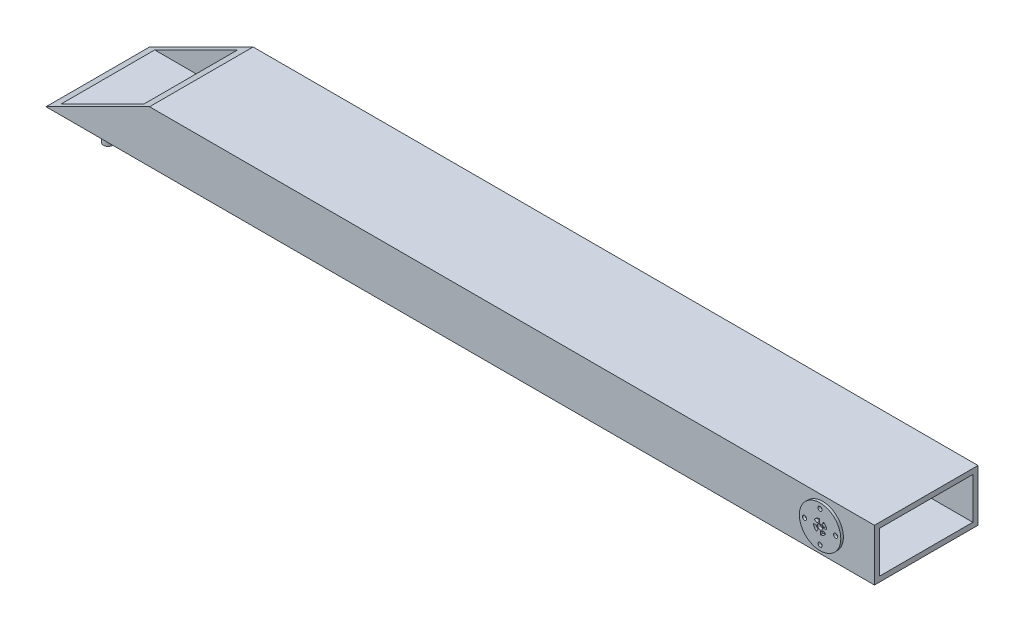
SolidWorks part; units mm, degrees
ref_plane "Front Plane" through (0, 0, 0) normal (0, 0, 1) x (1, 0, 0)
ref_plane "Top Plane" through (0, 0, 0) normal (0, 1, 0) x (1, 0, 0)
ref_plane "Right Plane" through (0, 0, 0) normal (1, 0, 0) x (0, 0, -1)
sketch "Sketch2" plane through (0, 0, 0) normal (0, 0, 1) x (1, 0, 0)
  line L0 (0, 0) -> (100, 0) construction
  line L1 (0, 0) -> (-1500, 0) construction
  line L2 (100, 0) -> (100, -50)
  line L3 (100, -50) -> (-1500, -50)
  line L4 (-1500, -50) -> (-1300, 50)
  line L5 (100, 0) -> (100, 50)
  line L6 (100, 50) -> (-1300, 50)
  circle A0 centre (0, 0) radius 20.25
  dimension "D1" = 40.5
  dimension "D2" = 100
  dimension "D3" = 1500
  dimension "D4" = 50
  dimension "D5" = 50
  dimension "D6" = 1400
extrude "Boss-Extrude1" add sketch "Sketch2" along normal blind 200
sketch "Sketch3" plane through (0, 0, 200) normal (0, 0, 1) x (1, 0, 0)
  line L0 (0, 0) -> (-30, 0) construction
  circle A0 centre (0, 0) radius 5
  circle A1 centre (0, 0) radius 40
  circle A2 centre (-30, 0) radius 4
  circle A3 centre (0, 30) radius 4
  circle A4 centre (30, 0) radius 4
  circle A5 centre (0, -30) radius 4
  point P15 (0, 0)
  dimension "D1" = 10
  dimension "D3" = 8
  dimension "D4" = 80
  dimension "D2" = 30
  dimension "D5" = 4
extrude "Boss-Extrude2" add sketch "Sketch3" along normal blind 5
sketch "Sketch4" plane through (0, 0, 200) normal (0, 0, 1) x (1, 0, 0)
  line L3 (-0.95, 6.8013) -> (-0.95, 12.9006)
  line L4 (-5.7779, 3.7115) -> (-11.074, 6.6854)
  line L5 (6.8013, 0.95) -> (12.9006, 0.95)
  line L6 (3.7115, 5.7779) -> (6.6854, 11.074)
  line L7 (0.95, -6.8013) -> (0.95, -12.9006)
  line L8 (5.7779, -3.7115) -> (11.074, -6.6854)
  line L9 (-6.8013, -0.95) -> (-12.9006, -0.95)
  line L10 (-3.7115, -5.7779) -> (-6.6854, -11.074)
  arc A3 (-0.95, 12.9006) -> (-11.074, 6.6854) centre (0, 0) ccw
  arc A4 (-0.95, 6.8013) -> (-5.7779, 3.7115) centre (0, 0) ccw
  arc A5 (12.9006, 0.95) -> (6.6854, 11.074) centre (0, 0) ccw
  arc A6 (6.8013, 0.95) -> (3.7115, 5.7779) centre (0, 0) ccw
  arc A7 (0.95, -12.9006) -> (11.074, -6.6854) centre (0, 0) ccw
  arc A8 (0.95, -6.8013) -> (5.7779, -3.7115) centre (0, 0) ccw
  arc A9 (-12.9006, -0.95) -> (-6.6854, -11.074) centre (0, 0) ccw
  arc A10 (-6.8013, -0.95) -> (-3.7115, -5.7779) centre (0, 0) ccw
  point P23 (0, 0)
  dimension "D2" = 4
extrude "Cut-Extrude5" cut sketch "Sketch4" against normal through all both and the other way through all
sketch "Sketch5" plane through (100, 0, 0) normal (1, 0, 0) x (0, 0, -1)
  line L0 (-200, 40) -> (-200, -40) construction
  line L1 (-190, 40) -> (-10, 40)
  line L2 (-190, 40) -> (-190, -40)
  line L3 (-190, -40) -> (-10, -40)
  line L4 (-10, 40) -> (-10, -40)
  line L5 (-200, -50) -> (0, -50) construction
  line L6 (-200, 50) -> (0, 50) construction
  dimension "D1" = 10
  dimension "D2" = 10
  dimension "D3" = 10
  dimension "D4" = 10
extrude "Cut-Extrude6" cut sketch "Sketch5" against normal through all
sketch "Sketch6" plane through (0, -40, 0) normal (0, 1, 0) x (1, 0, 0)
  line L0 (-1480, -100) -> (-1348.8369, -100) construction
  line L1 (-1480, -190) -> (-1480, -10) construction
  circle A0 centre (-1430, -150) radius 9
  circle A1 centre (-1430, -50) radius 9
  dimension "D1" = 50
  dimension "D3" = 18
  dimension "D4" = 18
  dimension "D2" = 50
  dimension "D5" = 50
  dimension "D6" = 50
extrude "Boss-Extrude3" add sketch "Sketch6" against normal blind 60
